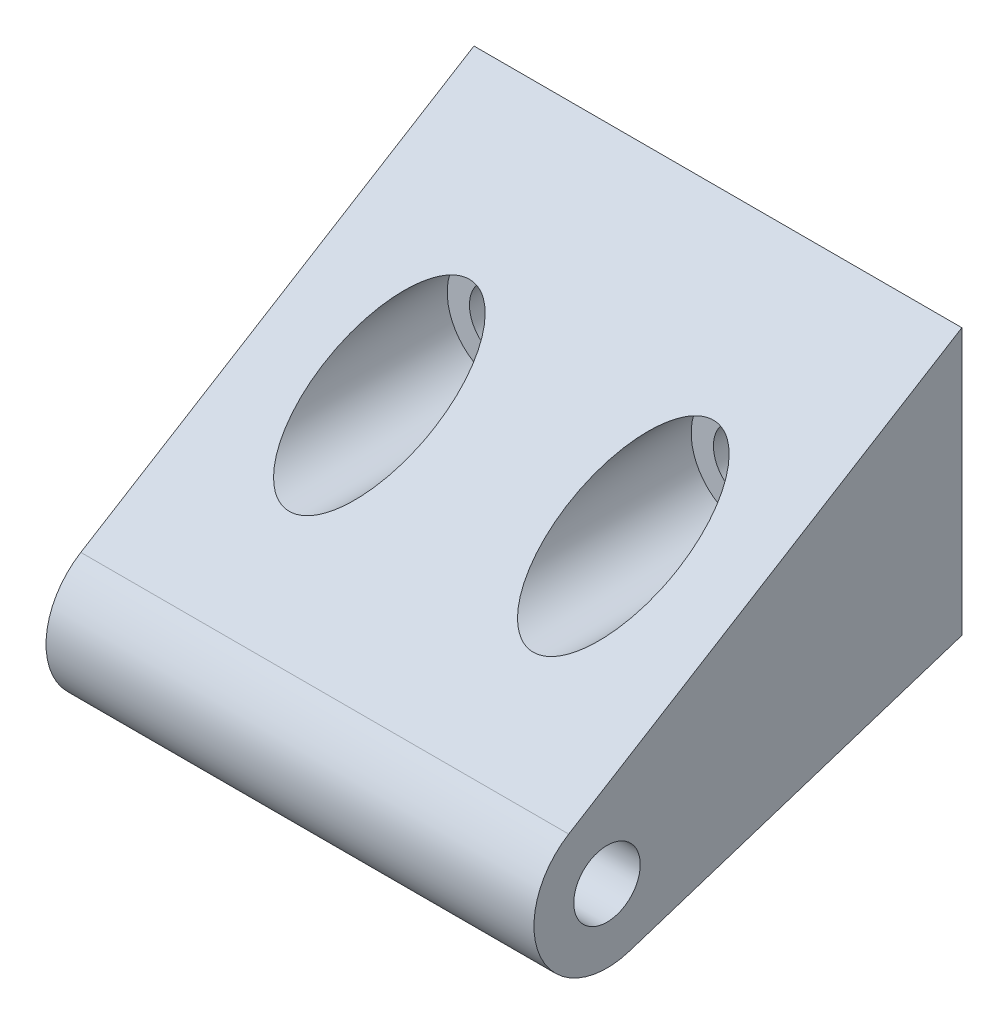
SolidWorks part; units mm, degrees
material "AISI 1035 Steel (SS)"
ref_plane "Front Plane" through (0, 0, 0) normal (0, 0, 1) x (1, 0, 0)
ref_plane "Top Plane" through (0, 0, 0) normal (0, 1, 0) x (1, 0, 0)
ref_plane "Right Plane" through (0, 0, 0) normal (1, 0, 0) x (0, 0, -1)
sketch "Sketch1" plane through (0, 0, 0) normal (1, 0, 0) x (0, 0, -1)
  line L0 (15.5626, 11.0617) -> (15.5626, 1.3716)
  line L1 (15.5626, 1.3716) -> (3.4725, -2.5285)
  line L2 (1.2644, 2.2627) -> (15.5626, 11.0617)
  circle A0 centre (2.6568, 0) radius 1.209
  arc A1 (1.2644, 2.2627) -> (3.4725, -2.5285) centre (2.6568, 0) ccw
  dimension "D1" = 12.9057
  dimension "D2" = 11.0617
  dimension "D4" = 2.6568
  dimension "D5" = 2.4181
  dimension "D3" = 9.6901
extrude "Boss-Extrude1" add sketch "Sketch1" against normal blind 17.7444
sketch "Sketch5" plane through (0, 0, 0) normal (0, 0, 1) x (1, 0, 0)
  line L0 (-17.7444, 11.0617) -> (-17.7444, 2.2627) construction
  line L1 (-17.7444, 11.0617) -> (0, 11.0617) construction
  circle A0 centre (-13.3096, 6.2154) radius 2.0168
  circle A1 centre (-4.4374, 6.2154) radius 2.0168
  dimension "D1" = 4.0335
  dimension "D2" = 4.0335
  dimension "D3" = 8.8722
  dimension "D4" = 4.4348
  dimension "D5" = 4.8463
  dimension "D6" = 4.8463
extrude "Cut-Extrude5" cut sketch "Sketch5" against normal blind 12.1724
sketch "Sketch6" plane through (0, 0, -12.1724) normal (0, 0, 1) x (1, 0, 0)
  circle A0 centre (-13.3096, 6.2154) radius 1.209
  circle A1 centre (-4.4374, 6.2154) radius 1.209
extrude "Cut-Extrude6" cut sketch "Sketch6" against normal through all
